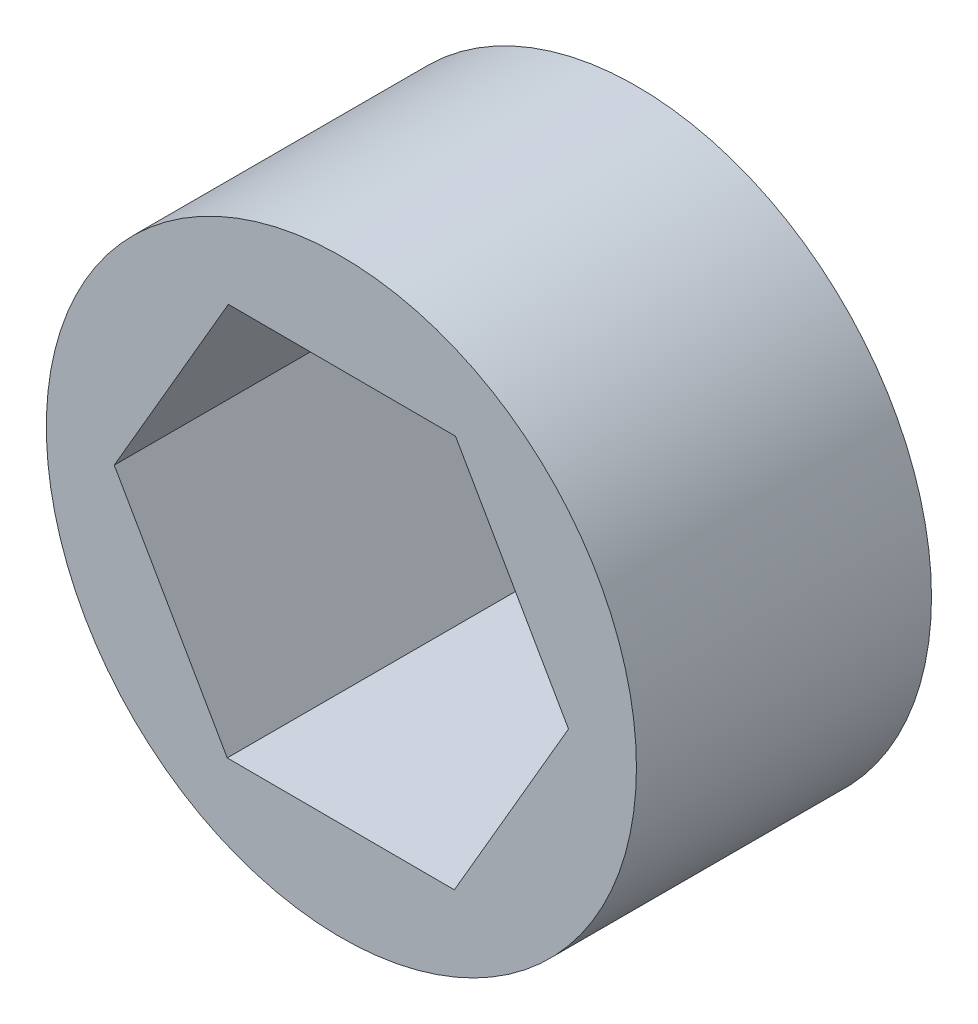
SolidWorks part; units mm, degrees
material "PET"
ref_plane "Front Plane" through (0, 0, 0) normal (0, 0, 1) x (1, 0, 0)
ref_plane "Top Plane" through (0, 0, 0) normal (0, 1, 0) x (1, 0, 0)
ref_plane "Right Plane" through (0, 0, 0) normal (1, 0, 0) x (0, 0, -1)
sketch "Sketch1" plane through (0, 0, 0) normal (0, 0, 1) x (1, 0, 0)
  line L1 (3.647, -6.361) -> (7.3323, -0.0221)
  line L2 (7.3323, -0.0221) -> (3.6853, 6.3389)
  line L3 (3.6853, 6.3389) -> (-3.647, 6.361)
  line L4 (-3.647, 6.361) -> (-7.3323, 0.0221)
  line L5 (-7.3323, 0.0221) -> (-3.6853, -6.3389)
  line L6 (-3.6853, -6.3389) -> (3.647, -6.361)
  circle A0 centre (0, 0) radius 9.525
  circle A1 centre (0, 0) radius 6.35 construction
  dimension "D1" = 19.05
  dimension "D2" = 12.7
extrude "Boss-Extrude1" add sketch "Sketch1" along normal blind 9.525
